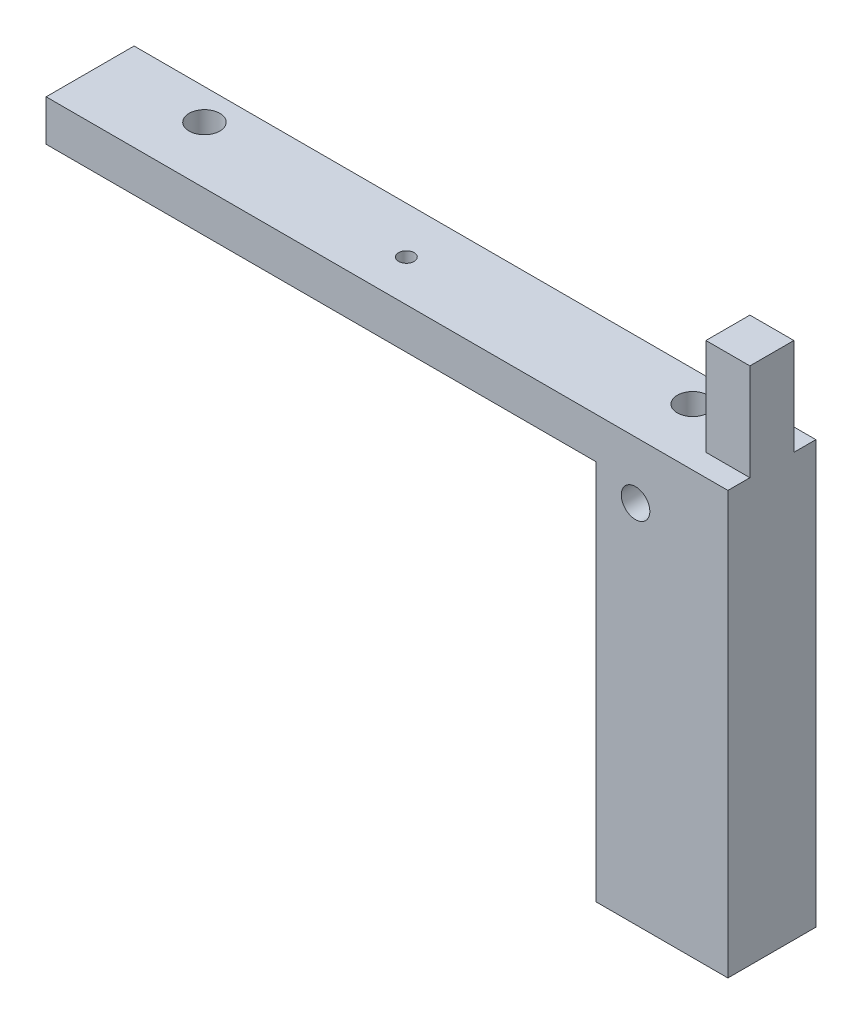
SolidWorks part; units mm, degrees
ref_plane "Front Plane" through (0, 0, 0) normal (0, 0, 1) x (1, 0, 0)
ref_plane "Top Plane" through (0, 0, 0) normal (0, 1, 0) x (1, 0, 0)
ref_plane "Right Plane" through (0, 0, 0) normal (1, 0, 0) x (0, 0, -1)
sketch "Sketch3" plane through (0, 0, 0) normal (0, 0, 1) x (1, 0, 0)
  line L0 (0, 0) -> (0, -5)
  line L1 (0, -5) -> (20, -5)
  line L2 (20, -5) -> (20, -25)
  line L3 (0, 0) -> (20, 0)
  line L4 (20, 0) -> (20, 22.02)
  line L5 (20, 22.02) -> (30, 22.02)
  line L6 (30, 22.02) -> (30, -25)
  line L7 (30, -25) -> (20, -25)
  dimension "D1" = 20
  dimension "D2" = 20
  dimension "D3" = 20
  dimension "D4" = 5
  dimension "D5" = 10
  dimension "D6" = 22.02
extrude "Boss-Extrude3" add sketch "Sketch3" along normal blind 10
sketch "Sketch5" plane through (0, 0, 10) normal (0, 0, 1) x (1, 0, 0)
  line L5 (0, 0) -> (30, 0)
  line L6 (0, 0) -> (0, -25)
  line L7 (0, -25) -> (30, -25)
  line L8 (30, 0) -> (30, -25)
extrude "Boss-Extrude5" add sketch "Sketch5" along normal blind 5
sketch "Sketch7" plane through (0, 0, 0) normal (0, 0, -1) x (-1, 0, 0)
  line L0 (-20, 0) -> (-30, 0)
  line L1 (-30, 0) -> (-30, -25)
  line L2 (-30, -25) -> (-20, -25)
  line L3 (-20, -25) -> (-20, -5)
  line L4 (-20, -5) -> (0, -5)
  line L5 (0, -5) -> (0, 0)
  line L6 (0, 0) -> (-20.7589, 0)
  line M8 (0, 0) -> (-20, 0)
  line M11 (-30, 22.02) -> (-30, -25)
  line M12 (-30, -25) -> (-20, -25)
  line M13 (-20, -25) -> (-20, -5)
  line M14 (-20, -5) -> (0, -5)
  line M15 (0, -5) -> (0, 0)
extrude "Boss-Extrude7" add sketch "Sketch7" along normal blind 5 contours L0 M8 M11 M12 M13 M14 M15
sketch "Sketch10" plane through (0, -25, 0) normal (0, -1, 0) x (1, 0, 0)
  line L0 (0, 10) -> (20, 10)
  line L1 (20, 10) -> (20, -5)
  line L2 (30, -5) -> (20, -5) construction
  line L3 (20, -5) -> (30, -5)
  line L4 (30, -5) -> (30, 15)
  line L5 (30, 15) -> (0, 15)
  line L6 (0, 15) -> (0, 10)
extrude "Boss-Extrude8" add sketch "Sketch10" along normal up to surface (71 mm away)
sketch "Sketch11" plane through (0, 0, 0) normal (-1, 0, 0) x (0, 0, 1)
  line L0 (15, 0) -> (15, -96) construction
  line L1 (-5, 0) -> (15, 0)
  line L2 (-5, 0) -> (-5, -5)
  line L3 (-5, -5) -> (10, -5)
  line L4 (15, 0) -> (15, -5)
  line L5 (10, -5) -> (10, -96) construction
  line L6 (15, 0) -> (10, 0)
  line L7 (15, 0) -> (15, -9.3485)
  line L8 (15, -9.3485) -> (10, -9.3485)
  line L9 (10, -4.5368) -> (10, -9.3485)
extrude "Boss-Extrude9" add sketch "Sketch11" along normal blind 125
sketch "Sketch12" plane through (0, 0, 15) normal (0, 0, 1) x (1, 0, 0)
  circle A0 centre (9, -13) radius 3.25
extrude "Cut-Extrude1" cut sketch "Sketch12" against normal blind 15 and the other way blind 6
sketch "Sketch13" plane through (0, 0, 0) normal (0, 1, 0) x (1, 0, 0)
  line L1 (-125, -15) -> (-125, 5) construction
  circle A0 centre (-52.5, -5.5976) radius 1.75
  dimension "D1" = 72.5
  dimension "D2" = 3.5
extrude "Cut-Extrude2" cut sketch "Sketch13" against normal blind 15 and the other way blind 5
sketch "Sketch14" plane through (0, 0, 0) normal (0, 1, 0) x (1, 0, 0)
  circle A0 centre (-102, -2) radius 3.5
extrude "Cut-Extrude3" cut sketch "Sketch14" against normal blind 10
sketch "Sketch15" plane through (0, 0, 0) normal (0, 1, 0) x (1, 0, 0)
  circle A0 centre (9, -2) radius 3.5
extrude "Cut-Extrude4" cut sketch "Sketch15" against normal blind 10
